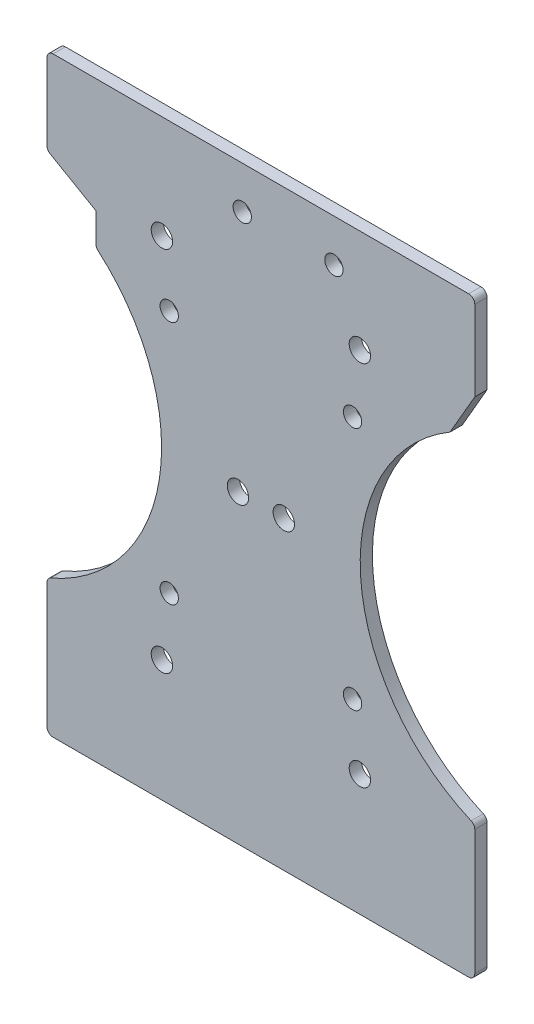
SolidWorks part; units mm, degrees
material "环氧板3240"
ref_plane "前视基准面" through (0, 0, 0) normal (0, 0, 1) x (1, 0, 0)
ref_plane "上视基准面" through (0, 0, 0) normal (0, 1, 0) x (1, 0, 0)
ref_plane "右视基准面" through (0, 0, 0) normal (1, 0, 0) x (0, 0, -1)
other "Configuration Table"
sketch "草图1" plane through (0, 0, 0) normal (0, 0, 1) x (1, 0, 0)
  line L0 (-35, -20) -> (35, -20) construction
  line L1 (-35, -46.9201) -> (35, -46.9201)
  line L3 (-35, 46.9201) -> (35, 46.9201) construction
  line L5 (-35, -46.9201) -> (35, 46.9201) construction
  line L6 (-35, 46.9201) -> (35, -46.9201) construction
  line L7 (-46.25, 0) -> (46.25, 0) construction
  line L8 (-46.25, 0) -> (-16.198, 30.052) construction
  line L9 (-46.25, 0) -> (-16.198, -30.052) construction
  line L10 (0, 46.9201) -> (0, -46.9201) construction
  line L11 (-46.25, 48.25) -> (-46.25, -48.25) construction
  line L12 (-35, 46.9201) -> (-35, 27.8107)
  line L13 (-35, -27.8107) -> (-35, -46.9201)
  line L14 (35, -27.8107) -> (35, -46.9201)
  line L15 (35, 46.9201) -> (35, 27.8107)
  line L16 (-35, 20) -> (35, 20) construction
  line L22 (0, 13.7477) -> (0, -13.7477) construction
  line L23 (0, 13.7477) -> (0, -13.7477) construction
  line L24 (-3.05, 40) -> (11.95, 40) construction
  line L26 (-10.9, 51.9201) -> (16.8, 51.9201)
  line L28 (35, 32.8107) -> (30.9582, 25.8101)
  line L29 (-35, 32.8107) -> (-27, 28.1919)
  line L30 (-27, 28.1919) -> (-27, 23.0095)
  line L31 (-10.9, 51.9201) -> (-10.9, 46.9201)
  line L32 (16.8, 51.9201) -> (16.8, 46.9201)
  line L33 (-10.9, 46.9201) -> (-35, 46.9201)
  line L34 (16.8, 46.9201) -> (35, 46.9201)
  line L35 (4.45, 46.9201) -> (4.45, 32.28) construction
  arc A0 (-46.25, -42.5) -> (-46.25, 42.5) centre (-46.25, 0) ccw construction
  arc A1 (35, 40.984) -> (35, -40.984) centre (46.25, 0) ccw construction
  circle A2 centre (-3.75, 0) radius 1.75
  circle A3 centre (-16.198, 30.052) radius 1.75
  circle A4 centre (-16.198, -30.052) radius 1.75
  circle A5 centre (-16.198, 30.052) radius 1.75
  circle A6 centre (-16.198, -30.052) radius 1.75
  circle A7 centre (16.198, -30.052) radius 1.75
  circle A8 centre (3.75, 0) radius 1.75
  circle A9 centre (16.198, 30.052) radius 1.75
  arc A10 (-35, -27.8107) -> (-35, 27.8107) centre (-46.25, 0) ccw
  arc A11 (35, 27.8107) -> (35, -27.8107) centre (46.25, 0) ccw
  arc A12 (-35, -46.9201) -> (-35, 46.9201) centre (-46.25, 0) ccw construction
  arc A13 (35, 46.9201) -> (35, -46.9201) centre (46.25, 0) ccw construction
  circle A15 centre (0, -20) radius 1.5 construction
  circle A18 centre (-3.05, 40) radius 1.5
  circle A20 centre (11.95, 40) radius 1.5
  circle A21 centre (0, 20) radius 1.5 construction
  point P4 (0, 0)
  dimension "D1" = 85
  dimension "D2" = 45
  dimension "D4" = 3.5
  dimension "D5" = 96.5
  dimension "D6" = 60
  dimension "D9" = 40
  dimension "D10" = 46.25
  dimension "D14" = 15
  dimension "D15" = 27.7
  dimension "D13" = 3
  dimension "D16" = 30
  dimension "D17" = 5
  dimension "D11" = 40
  dimension "D12" = 4.45
  dimension "D3" = 92.5
  dimension "D7" = 70
  dimension "D8" = 40
  dimension "D18" = 5
  dimension "D19" = 60
  dimension "D20" = 8
  dimension "D21" = 16.8
  dimension "D22" = 5
extrude "凸台-拉伸1" add sketch "草图1" along normal blind 2
sketch "草图2" plane through (0, 0, 0) normal (0, 0, -1) x (-1, 0, 0)
  line L1 (-16.8, 51.9201) -> (10.9, 51.9201)
  line L2 (-16.8, 51.9201) -> (-16.8, 46.9201)
  line L3 (-16.8, 46.9201) -> (10.9, 46.9201)
  line L4 (10.9, 51.9201) -> (10.9, 46.9201)
  line L5 (-16.8, 51.9201) -> (10.9, 46.9201) construction
  line L6 (-16.8, 46.9201) -> (10.9, 51.9201) construction
  point P6 (-2.95, 49.4201)
extrude "切除-拉伸1" cut sketch "草图2" against normal blind 10
sketch "草图3" plane through (0, 0, 0) normal (0, 0, -1) x (-1, 0, 0)
  line L0 (0, 20) -> (0, 0) construction
  line L1 (-3.75, 0) -> (3.75, 0) construction
  line L2 (-15, 20) -> (0, 20) construction
  circle A0 centre (-15, 20) radius 1.5
  circle A1 centre (-3.75, 0) radius 3.5 construction
  circle A2 centre (15, 20) radius 1.5
  circle A3 centre (15, -20) radius 1.5
  circle A4 centre (-15, -20) radius 1.5
  dimension "D1" = 7
  dimension "D2" = 3
  dimension "D3" = 15
  dimension "D4" = 7.5
  dimension "D5" = 20
extrude "切除-拉伸2" cut sketch "草图3" against normal blind 10
sketch "草图4" plane through (0, 0, 0) normal (0, 0, -1) x (-1, 0, 0)
  line L0 (0, 0) -> (0, -48.4201) construction
  line L1 (-35, -46.9201) -> (35, -46.9201)
  line L2 (-35, -46.9201) -> (-35, -49.9201)
  line L3 (-35, -49.9201) -> (35, -49.9201)
  line L4 (35, -46.9201) -> (35, -49.9201)
  line L5 (-35, -46.9201) -> (35, -49.9201) construction
  line L6 (-35, -49.9201) -> (35, -46.9201) construction
  line L7 (35, -46.9201) -> (-35, -46.9201) construction
  point P4 (0, -48.4201)
  dimension "D1" = 3
  dimension "D2" = 70
extrude "凸台-拉伸2" add sketch "草图4" against normal blind 2
fillet "圆角1" radius 1 8 edges at (35, -27.8107, 1) (35, -49.9201, 1) (-35, -49.9201, 1) (-35, -27.8107, 1) (-27, 23.0095, 1) (-35, 32.8107, 1) (-35, 46.9201, 1) (35, 46.9201, 1)
